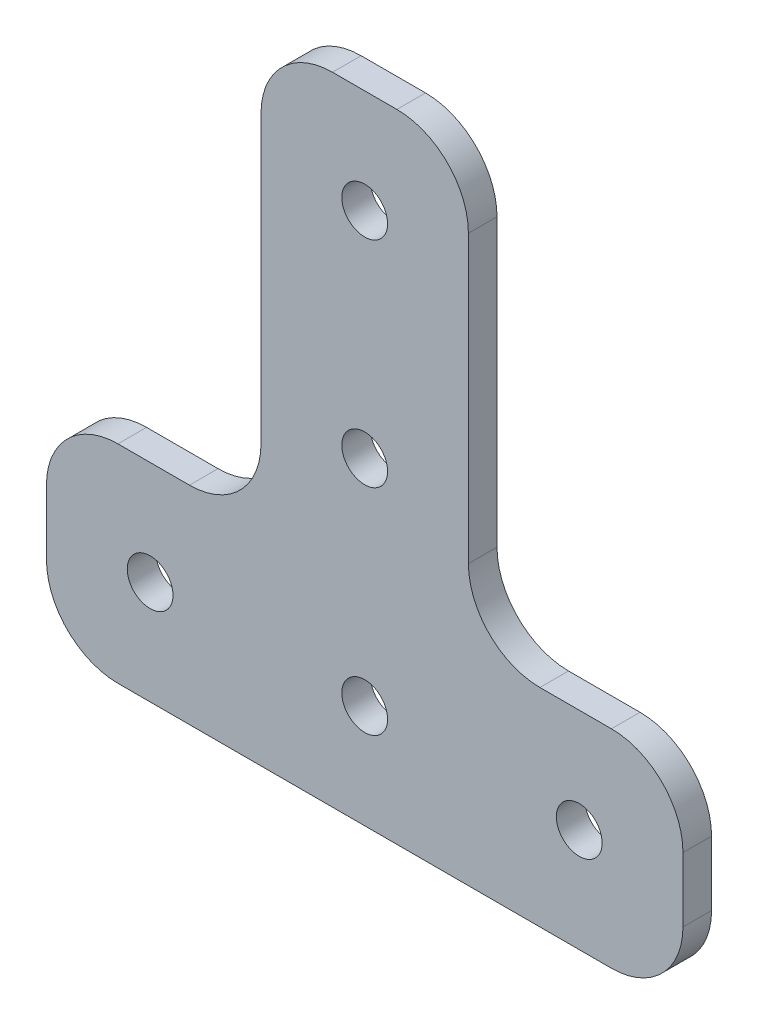
SolidWorks part; units mm, degrees
ref_plane "Front Plane" through (0, 0, 0) normal (0, 0, 1) x (1, 0, 0)
ref_plane "Top Plane" through (0, 0, 0) normal (0, 1, 0) x (1, 0, 0)
ref_plane "Right Plane" through (0, 0, 0) normal (1, 0, 0) x (0, 0, -1)
sketch "Sketch1" plane through (0, 0, 0) normal (0, 0, 1) x (1, 0, 0)
  line L0 (0, 62.6445) -> (0, -35.67) construction
  line L1 (-22.25, 0) -> (22.25, 0)
  line L2 (-22.25, 0) -> (-22.25, 14.5)
  line L3 (-22.25, 14.5) -> (-7.25, 14.5)
  line L4 (22.25, 0) -> (22.25, 14.5)
  line L5 (-22.25, 7.25) -> (22.25, 7.25) construction
  line L6 (0, 44.5) -> (0, 0) construction
  line L7 (7.25, 14.5) -> (22.25, 14.5)
  line L8 (-7.25, 44.5) -> (7.25, 44.5)
  line L9 (-7.25, 44.5) -> (-7.25, 14.5)
  line L10 (0, -54.6431) -> (0, 54.6431) construction
  line L11 (7.25, 44.5) -> (7.25, 14.5)
  circle A0 centre (0, 7.25) radius 1.6
  circle A1 centre (15, 7.25) radius 1.6
  circle A2 centre (0, 22.25) radius 1.6
  circle A3 centre (0, 37.25) radius 1.6
  circle A4 centre (-15, 7.25) radius 1.6
  point P0 (0, 0)
  dimension "D5" = 3.2
  dimension "D1" = 14.5
  dimension "D2" = 44.5
  dimension "D3" = 44.5
  dimension "D4" = 15
  dimension "D6" = 15
  dimension "D7" = 15
extrude "Boss-Extrude1" add sketch "Sketch1" along normal blind 2
fillet "Fillet1" radius 5 8 edges at (-7.25, 44.5, 1) (7.25, 44.5, 1) (22.25, 0, 1) (22.25, 14.5, 1) (-22.25, 0, 1) (-22.25, 14.5, 1) (7.25, 14.5, 1) (-7.25, 14.5, 1)
